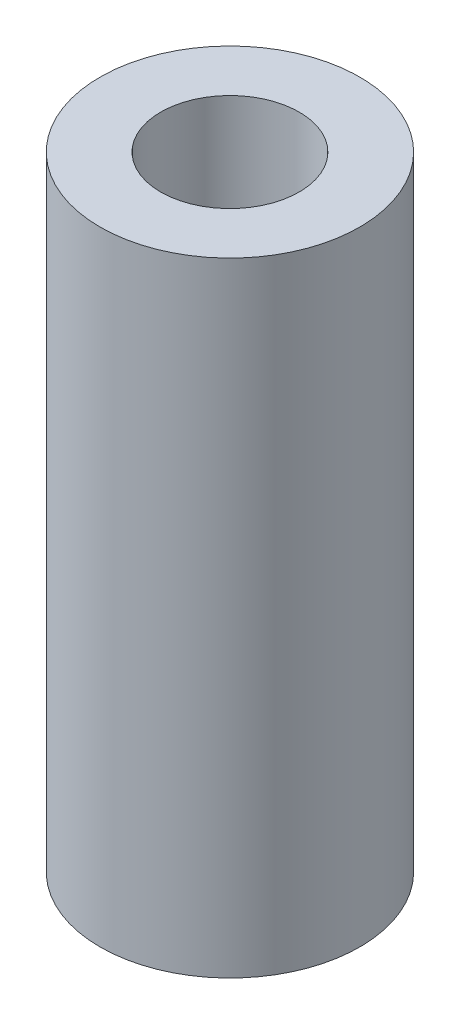
SolidWorks part; units mm, degrees
ref_plane "Face" through (0, 0, 0) normal (0, 0, 1) x (1, 0, 0)
ref_plane "Dessus" through (0, 0, 0) normal (0, 1, 0) x (1, 0, 0)
ref_plane "Droite" through (0, 0, 0) normal (1, 0, 0) x (0, 0, -1)
sketch "Esquisse1" plane through (0, 0, 0) normal (0, 1, 0) x (1, 0, 0)
  circle A0 centre (0, 0) radius 7.5
  circle A1 centre (0, 0) radius 4
  dimension "D1" = 15
  dimension "D2" = 8
extrude "Extrusion1" add sketch "Esquisse1" along normal blind 36
